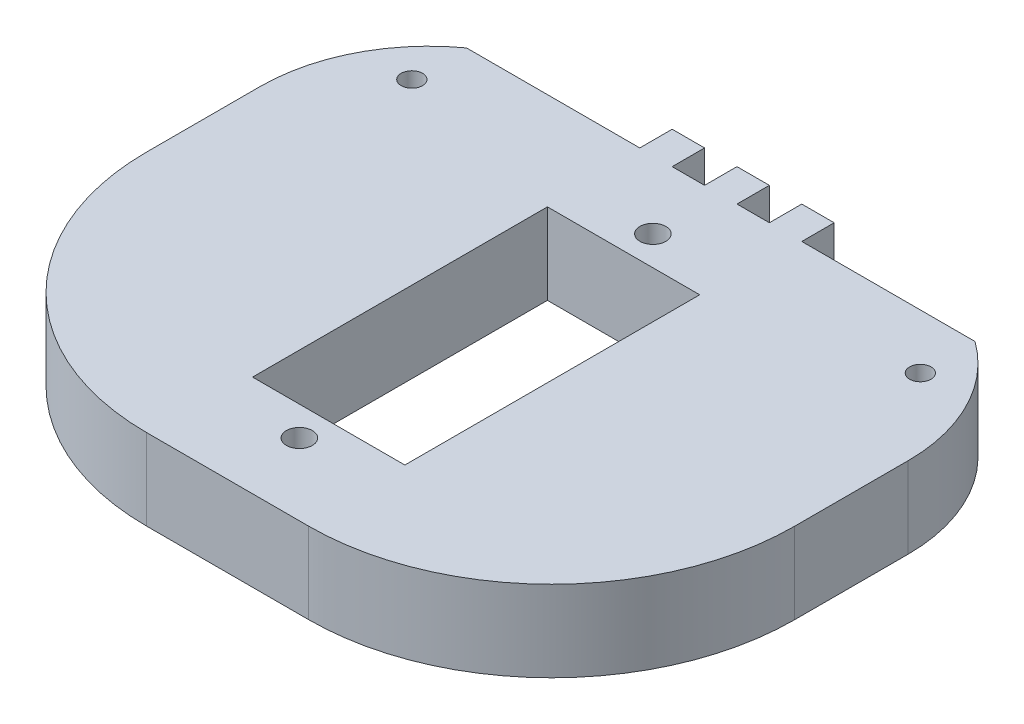
SolidWorks part; units mm, degrees
ref_plane "Front Plane" through (0, 0, 0) normal (0, 0, 1) x (1, 0, 0)
ref_plane "Top Plane" through (0, 0, 0) normal (0, 1, 0) x (1, 0, 0)
ref_plane "Right Plane" through (0, 0, 0) normal (1, 0, 0) x (0, 0, -1)
sketch "Sketch2" plane through (0, 0, 0) normal (0, 1, 0) x (1, 0, 0)
  line L0 (19.05, -6.35) -> (31.75, -6.35)
  line L1 (50.8, 12.7) -> (50.8, 21.59)
  line L3 (0, 12.7) -> (0, 21.59)
  line L5 (25.4, 24.6838) -> (31.369, 24.6838)
  line L6 (24.13, 34.8438) -> (26.67, 34.8438)
  line L7 (25.4, 24.6838) -> (19.431, 24.6838)
  line L8 (19.431, 24.6838) -> (19.431, 1.5698)
  line L9 (19.431, 1.5698) -> (31.369, 1.5698)
  line L10 (31.369, 1.5698) -> (31.369, 24.6838)
  line L11 (26.67, 34.8438) -> (26.67, 32.3038)
  line L13 (26.67, 32.3038) -> (29.21, 32.3038)
  line L14 (29.21, 32.3038) -> (29.21, 34.8438)
  line L15 (29.21, 34.8438) -> (31.75, 34.8438)
  line L16 (31.75, 34.8438) -> (31.75, 32.3038)
  line L17 (31.75, 32.3038) -> (45.3298, 32.3038)
  line L19 (19.05, 32.3038) -> (5.4702, 32.3038)
  line L20 (19.05, 34.8438) -> (19.05, 32.3038)
  line L21 (21.59, 34.8438) -> (19.05, 34.8438)
  line L22 (21.59, 32.3038) -> (21.59, 34.8438)
  line L23 (24.13, 32.3038) -> (21.59, 32.3038)
  line L24 (24.13, 34.8438) -> (24.13, 32.3038)
  circle A0 centre (45.3298, 28.0176) radius 0.8401
  circle A1 centre (25.4, 26.9838) radius 1.016
  arc A2 (0, 12.7) -> (19.05, -6.35) centre (19.05, 12.7) ccw
  arc A3 (31.75, -6.35) -> (50.8, 12.7) centre (31.75, 12.7) ccw
  circle A4 centre (5.4702, 28.0176) radius 0.8401
  arc A5 (0, 21.59) -> (5.4702, 32.3038) centre (13.2271, 21.59) cw
  arc A6 (50.8, 21.59) -> (45.3298, 32.3038) centre (37.5729, 21.59) ccw
  circle A7 centre (25.4, -0.7301) radius 1.016
  point P32 (25.4, 34.8438)
  dimension "D3" = 2.032
  dimension "D1" = 23.114
  dimension "D4" = 1.6802
  dimension "D6" = 1.6802
  dimension "D5" = 2.032
  dimension "D2" = 11.938
  dimension "D7" = 13.5798
  dimension "D8" = 13.5798
extrude "Boss-Extrude2" add sketch "Sketch2" along normal blind 6.35
